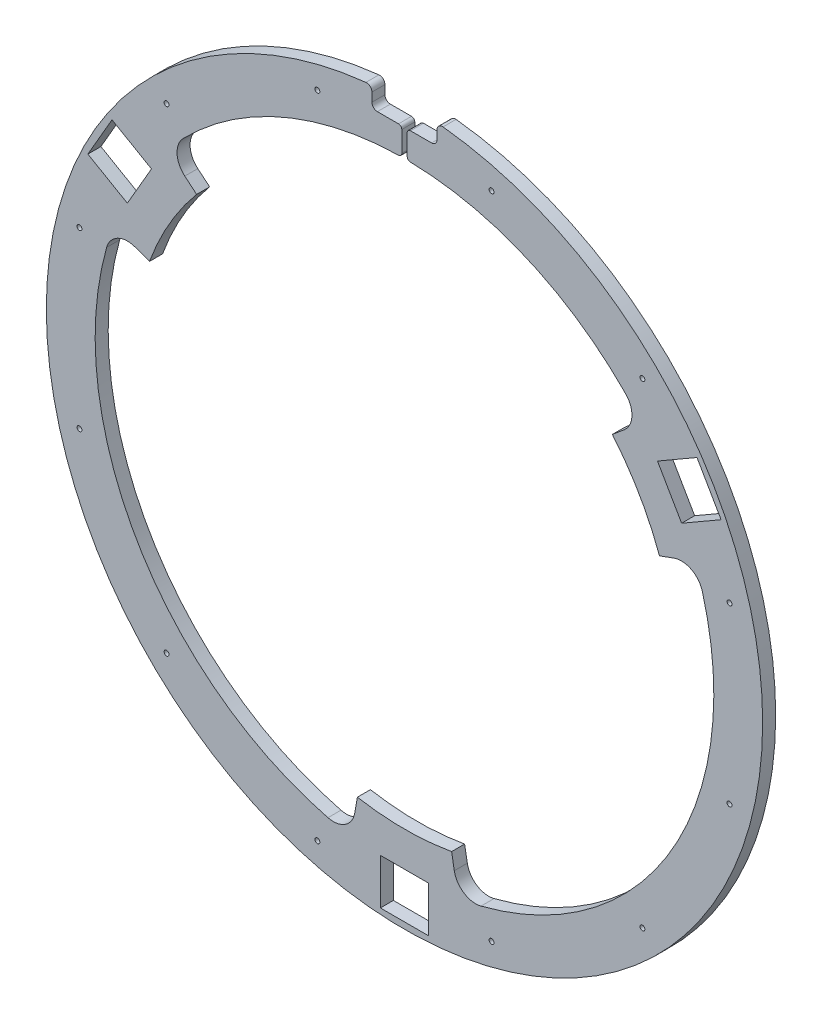
SolidWorks part; units mm, degrees
ref_plane "Front Plane" through (0, 0, 0) normal (0, 0, 1) x (1, 0, 0)
ref_plane "Top Plane" through (0, 0, 0) normal (0, 1, 0) x (1, 0, 0)
ref_plane "Right Plane" through (0, 0, 0) normal (1, 0, 0) x (0, 0, -1)
sketch "Sketch2" plane through (0, 0, -518.3606) normal (0, 0, 1) x (1, 0, 0)
  line L0 (0, 0) -> (0, 142.2716) construction
  line L1 (244.2192, 141) -> (0, 0) construction
  line L2 (22.225, -324) -> (22.225, -282)
  line L3 (22.225, -282) -> (-22.225, -282)
  line L4 (269.4797, 181.2474) -> (233.1067, 160.2474)
  line L5 (233.1067, 160.2474) -> (255.3317, 121.7526)
  line L6 (255.3317, 121.7526) -> (291.7047, 142.7526)
  line L7 (291.7047, 142.7526) -> (269.4797, 181.2474)
  line L8 (-22.225, -282) -> (-22.225, -324)
  line L9 (-22.225, -324) -> (22.225, -324)
  line L10 (-291.7047, 142.7526) -> (-255.3317, 121.7526)
  line L11 (-255.3317, 121.7526) -> (-233.1067, 160.2474)
  line L12 (-233.1067, 160.2474) -> (-269.4797, 181.2474)
  line L13 (-269.4797, 181.2474) -> (-291.7047, 142.7526)
  circle A0 centre (0, 0) radius 330
  circle A2 centre (0, 0) radius 250
  point P15 (0, 0)
  point P37 (-7.2575, -45.052)
  dimension "D1" = 660
  dimension "D6" = 500
  dimension "D2" = 42
  dimension "D3" = 44.45
  dimension "D4" = 282
  dimension "D5" = 60
  dimension "D7" = 3
extrude "Boss-Extrude1" add sketch "Sketch2" along normal blind 12
sketch "Sketch3" plane through (0, 0, -506.3606) normal (0, 0, 1) x (1, 0, 0)
  line L0 (191.5111, 160.6969) -> (202.4228, 169.8529)
  line L1 (-191.5111, 160.6969) -> (-202.4228, 169.8529)
  line L2 (43.412, -246.2019) -> (45.8855, -260.2297)
  line L4 (234.9232, 85.505) -> (248.3083, 90.3768)
  line L6 (0, 0) -> (0, 240.4153) construction
  line L7 (191.5111, 160.6969) -> (0, 0) construction
  line L8 (-234.9232, 85.505) -> (-248.3083, 90.3768)
  line L9 (-43.412, -246.2019) -> (-45.8855, -260.2297)
  arc A0 (203.874, 199.1492) -> (-203.874, 199.1492) centre (0, 0) ccw
  circle A1 centre (0, 0) radius 250 construction
  arc A2 (191.5111, 160.6969) -> (-191.5111, 160.6969) centre (0, 0) ccw
  arc A3 (-202.4228, 169.8529) -> (-203.874, 199.1492) centre (-189.5671, 185.1738) cw
  arc A4 (202.4228, 169.8529) -> (203.874, 199.1492) centre (189.5671, 185.1738) ccw
  circle A5 centre (0, 0) radius 330 construction
  arc A6 (70.5312, -276.1346) -> (274.4052, 76.9855) centre (0, 0) ccw
  arc A7 (43.412, -246.2019) -> (234.9232, 85.505) centre (0, 0) ccw
  arc A8 (248.3083, 90.3768) -> (274.4052, 76.9855) centre (255.1487, 71.583) cw
  arc A9 (45.8855, -260.2297) -> (70.5312, -276.1346) centre (65.5817, -256.7568) ccw
  arc A10 (-274.4052, 76.9855) -> (-70.5312, -276.1346) centre (0, 0) ccw
  arc A11 (-234.9232, 85.505) -> (-43.412, -246.2019) centre (0, 0) ccw
  arc A12 (-45.8855, -260.2297) -> (-70.5312, -276.1346) centre (-65.5817, -256.7568) cw
  arc A13 (-248.3083, 90.3768) -> (-274.4052, 76.9855) centre (-255.1487, 71.583) ccw
  point P33 (0, 0)
  dimension "D1" = 45
  dimension "D3" = 20
  dimension "D2" = 100
  dimension "D4" = 3
extrude "Cut-Extrude1" cut sketch "Sketch3" against normal blind 12
sketch "Sketch5" plane through (0, 0, -506.3606) normal (0, 0, 1) x (1, 0, 0)
  line L0 (0, 0) -> (0, 370) construction
  line L1 (30, 370) -> (30, 310)
  line L2 (30, 370) -> (-30, 370)
  line L4 (30, 310) -> (-30, 310)
  line L5 (-30, 370) -> (-30, 310)
  dimension "D1" = 310
  dimension "D2" = 60
  dimension "D3" = 60
extrude "Cut-Extrude2" cut sketch "Sketch5" against normal blind 12
fillet "Fillet1" radius 5 4 edges at (30, 310, -512.3606) (30, 328.6335, -512.3606) (-30, 328.6335, -512.3606) (-30, 310, -512.3606)
sketch "Sketch6" plane through (0, 0, -506.3606) normal (0, 0, 1) x (1, 0, 0)
  line L0 (0, 0) -> (0, 347.7499) construction
  line L2 (-2.5, 310) -> (2.5, 310)
  line L3 (-25, 310) -> (25, 310) construction
  line L4 (-2.5, 280) -> (2.5, 280)
  line L5 (2.5, 310) -> (2.5, 280)
  line L6 (-2.5, 310) -> (-2.5, 280)
  dimension "D1" = 5
  dimension "D2" = 30
extrude "Cut-Extrude3" cut sketch "Sketch6" against normal blind 12
fillet "Fillet2" radius 3 4 edges at (-2.5, 310, -512.3606) (2.5, 310, -512.3606) (-2.5, 284.989, -512.3606) (2.5, 284.989, -512.3606)
hole_wizard "CSK for M4 Flat Head Machine Screw" positions "Sketch7" profile "Sketch8" countersink size "M4" standard "ANSI Metric" end condition through all
sketch "Sketch7" plane through (0, 0, -530.3606) normal (0, 0, -1) x (1, 0, 0)
  line L0 (80.2339, 299.437) -> (0, 0) construction
  line L2 (0, 0) -> (0, 423.7069) construction
  circle A0 centre (0, 0) radius 310 construction
  point P0 (80.2339, 299.437)
  point P21 (219.2031, 219.2031)
  point P22 (299.437, 80.2339)
  point P23 (299.437, -80.2339)
  point P24 (219.2031, -219.2031)
  point P25 (80.2339, -299.437)
  point P26 (-80.2339, -299.437)
  point P27 (-219.2031, -219.2031)
  point P28 (-299.437, -80.2339)
  point P29 (-299.437, 80.2339)
  point P30 (-219.2031, 219.2031)
  point P31 (-80.2339, 299.437)
  point P32 (0, 0)
sketch "Sketch8" plane through (80.2339, -299.437, -530.3606) normal (1, 0, 0) x (0, 1, 0)
  line L0 (0, 0) -> (0, 24)
  line L1 (0, 24) -> (2.25, 24)
  line L2 (2.25, 24) -> (2.25, 2.45)
  line L3 (2.25, 2.45) -> (4.7, 0)
  line L4 (4.7, 0) -> (0, 0)
  line L5 (-2.25, 2.45) -> (-4.7, 0) construction
  line L6 (0, -6.35) -> (0, 107.95) construction
  dimension "Thru Hole Dia." = 4.5
  dimension "Thru Hole Depth" = 24
  dimension "Near C'Sink Dia." = 9.4
  dimension "Near C'Sink Angle" = 90
sketch "Sketch9" plane through (0, 0, -506.3606) normal (0, 0, 1) x (1, 0, 0)
  line L0 (0, 355) -> (0, 0)
  line L1 (0, 0) -> (307.439, -177.5)
  arc A0 (0, 355) -> (307.439, -177.5) centre (0, 0) cw
  dimension "D1" = 120
  dimension "D2" = 355
extrude "Cut-Extrude4" [suppressed] cut sketch "Sketch9" against normal blind 12 flip side to cut
sketch "Sketch10" plane through (0, 0, -506.3606) normal (0, 0, 1) x (1, 0, 0)
  line L0 (0, 355) -> (0, 0)
  line L1 (0, 0) -> (-307.439, -177.5)
  arc A0 (0, 355) -> (-307.439, -177.5) centre (0, 0) ccw
  dimension "D1" = 120
  dimension "D2" = 355
extrude "Cut-Extrude5" [suppressed] cut sketch "Sketch10" against normal blind 12 flip side to cut
sketch "Sketch11" plane through (0, 0, -506.3606) normal (0, 0, 1) x (1, 0, 0)
  line L0 (0, 0) -> (-307.439, -177.5)
  line L1 (0, 0) -> (307.439, -177.5)
  line L2 (0, 0) -> (0, 353.0431) construction
  arc A0 (-307.439, -177.5) -> (307.439, -177.5) centre (0, 0) ccw
  dimension "D1" = 120
  dimension "D2" = 120
  dimension "D3" = 355
extrude "Cut-Extrude6" [suppressed] cut sketch "Sketch11" against normal blind 12 flip side to cut
